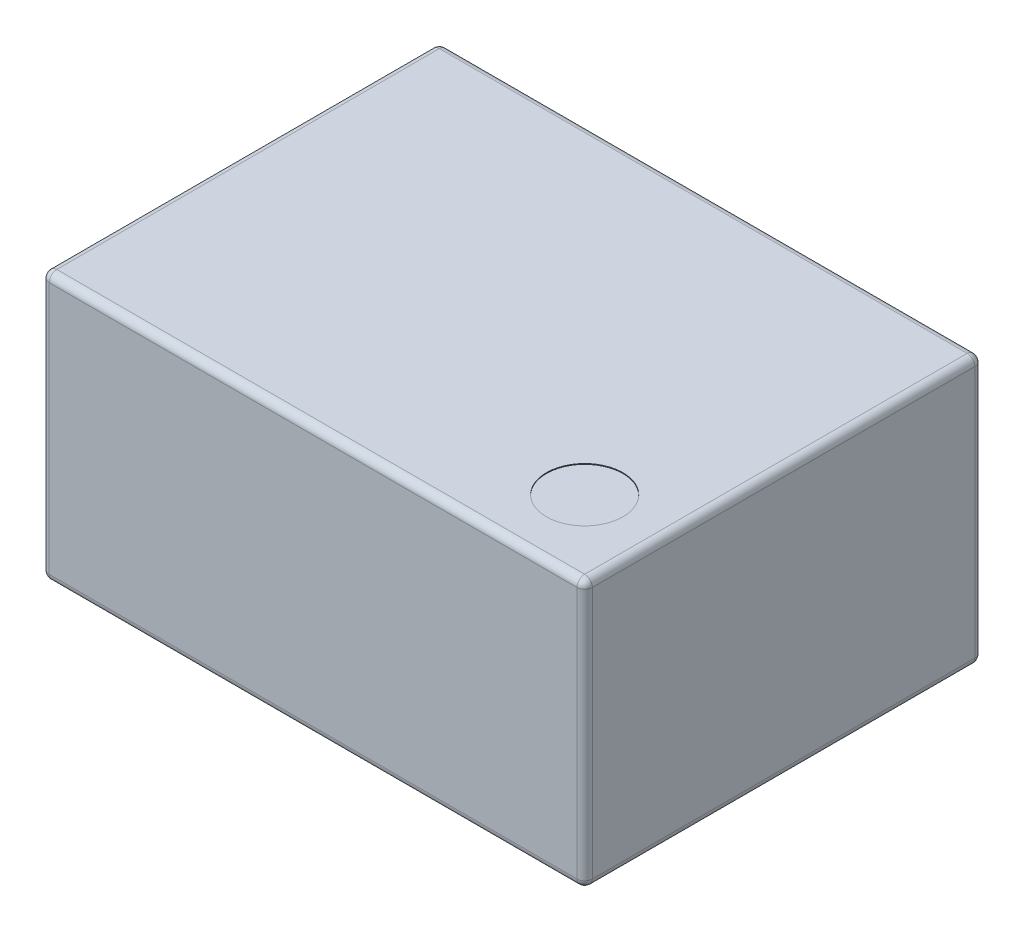
SolidWorks part; units mm, degrees
ref_plane "Front Plane" through (0, 0, 0) normal (0, 0, 1) x (1, 0, 0)
ref_plane "Top Plane" through (0, 0, 0) normal (0, 1, 0) x (1, 0, 0)
ref_plane "Right Plane" through (0, 0, 0) normal (1, 0, 0) x (0, 0, -1)
sketch "Sketch1" plane through (0, 0, 0) normal (0, 1, 0) x (1, 0, 0)
  line L1 (-3.55, 2.6) -> (3.55, 2.6)
  line L2 (-3.55, 2.6) -> (-3.55, -2.6)
  line L3 (-3.55, -2.6) -> (3.55, -2.6)
  line L4 (3.55, 2.6) -> (3.55, -2.6)
  line L5 (-3.55, 2.6) -> (3.55, -2.6) construction
  line L6 (-3.55, -2.6) -> (3.55, 2.6) construction
  point P0 (0, 0)
  dimension "D1" = 7.1
  dimension "D2" = 5.2
extrude "Boss-Extrude1" add sketch "Sketch1" along normal blind 3.5
fillet "Fillet1" radius 0.1 12 edges at (0, 0, -2.6) (-3.55, 0, 0) (0, 0, 2.6) (3.55, 0, 0) (3.55, 1.75, -2.6) (0, 3.5, -2.6) (3.55, 3.5, 0) (3.55, 1.75, 2.6) (-3.55, 1.75, 2.6) (-3.55, 1.75, -2.6) (-3.55, 3.5, 0) (0, 3.5, 2.6)
ref_plane "Plane1" through (0, 0, 1.27) normal (0, 0, 1) x (1, 0, 0)
sketch "Sketch2" plane through (0, 3.5, 0) normal (0, 1, 0) x (1, 0, 0)
  line L0 (3.45, -2.6) -> (-3.45, -2.6) construction
  line L1 (3.55, 2.5) -> (3.55, -2.5) construction
  circle A0 centre (2.55, -1.6) radius 0.5
  dimension "D3" = 1
  dimension "D1" = 1
  dimension "D2" = 1
extrude "Cut-Extrude1" cut sketch "Sketch2" against normal blind 0.01
